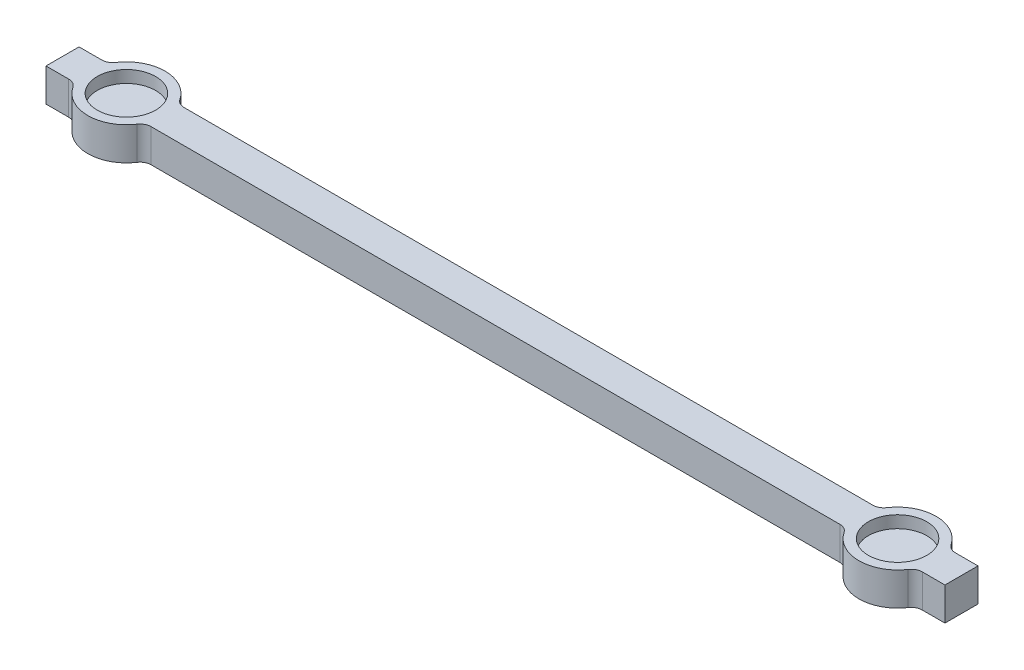
SolidWorks part; units mm, degrees
ref_plane "Front Plane" through (0, 0, 0) normal (0, 0, 1) x (1, 0, 0)
ref_plane "Top Plane" through (0, 0, 0) normal (0, 1, 0) x (1, 0, 0)
ref_plane "Right Plane" through (0, 0, 0) normal (1, 0, 0) x (0, 0, -1)
sketch "Sketch1" plane through (0, 0, 0) normal (0, 1, 0) x (1, 0, 0)
  line L0 (-40.8, 0) -> (40.8, 0) construction
  line L1 (-40.8, 3.5) -> (40.8, 3.5)
  line L2 (-40.8, 3.5) -> (-40.8, -3.5)
  line L3 (-40.8, -3.5) -> (40.8, -3.5)
  line L4 (40.8, 3.5) -> (40.8, -3.5)
  line L5 (-40.8, 3.5) -> (40.8, -3.5) construction
  line L6 (-40.8, -3.5) -> (40.8, 3.5) construction
  line L7 (0, 3.5) -> (0, -3.5) construction
  line L8 (-39.5, 3.5) -> (-39.5, -3.5) construction
  line L10 (40.8, 1.5) -> (-40.8, 1.5)
  line L11 (40.8, 1.5) -> (40.8, -1.5)
  line L12 (40.8, -1.5) -> (-40.8, -1.5)
  line L13 (-40.8, 1.5) -> (-40.8, -1.5)
  line L14 (40.8, 1.5) -> (-40.8, -1.5) construction
  line L15 (40.8, -1.5) -> (-40.8, 1.5) construction
  circle A0 centre (-35, 0) radius 2.5
  circle A1 centre (-35, 0) radius 3.5
  circle A2 centre (35, 0) radius 3.5
  point P0 (0, 0)
  point P15 (-37.5, 0)
  point P16 (0, 0)
  dimension "D3" = 5
  dimension "D1" = 81.6
  dimension "D2" = 7
  dimension "D4" = 1.3
  dimension "D5" = 2
  dimension "D6" = 3
extrude "Base shape" add sketch "Sketch1" along normal blind 3 contours A1 | L10 L13 L12 L11 | A2
sketch "Sketch2" plane through (0, 3, 0) normal (0, 1, 0) x (1, 0, 0)
  circle A0 centre (-35, 0) radius 2.65
  circle A1 centre (35, 0) radius 2.65
  dimension "D1" = 5.3
extrude "Magnet holes" cut sketch "Sketch2" against normal blind 1.1
fillet "Milling fillets" radius 1 8 edges at (31.8377, 1.5, -1.5) (38.1623, 1.5, -1.5) (-38.1623, 1.5, -1.5) (-31.8377, 1.5, -1.5) (31.8377, 1.5, 1.5) (38.1623, 1.5, 1.5) (-38.1623, 1.5, 1.5) (-31.8377, 1.5, 1.5)
sketch "Coordinate system sketch" plane through (0, 3, 0) normal (0, 1, 0) x (1, 0, 0)
  line L0 (35, -3.5) -> (40.8, -3.5) construction
  line L1 (40.8, -3.5) -> (40.8, -1.5) construction
  arc A0 (32.0898, -1.9444) -> (37.9102, -1.9444) centre (35, 0) ccw construction
  point P7 (0, 0)
